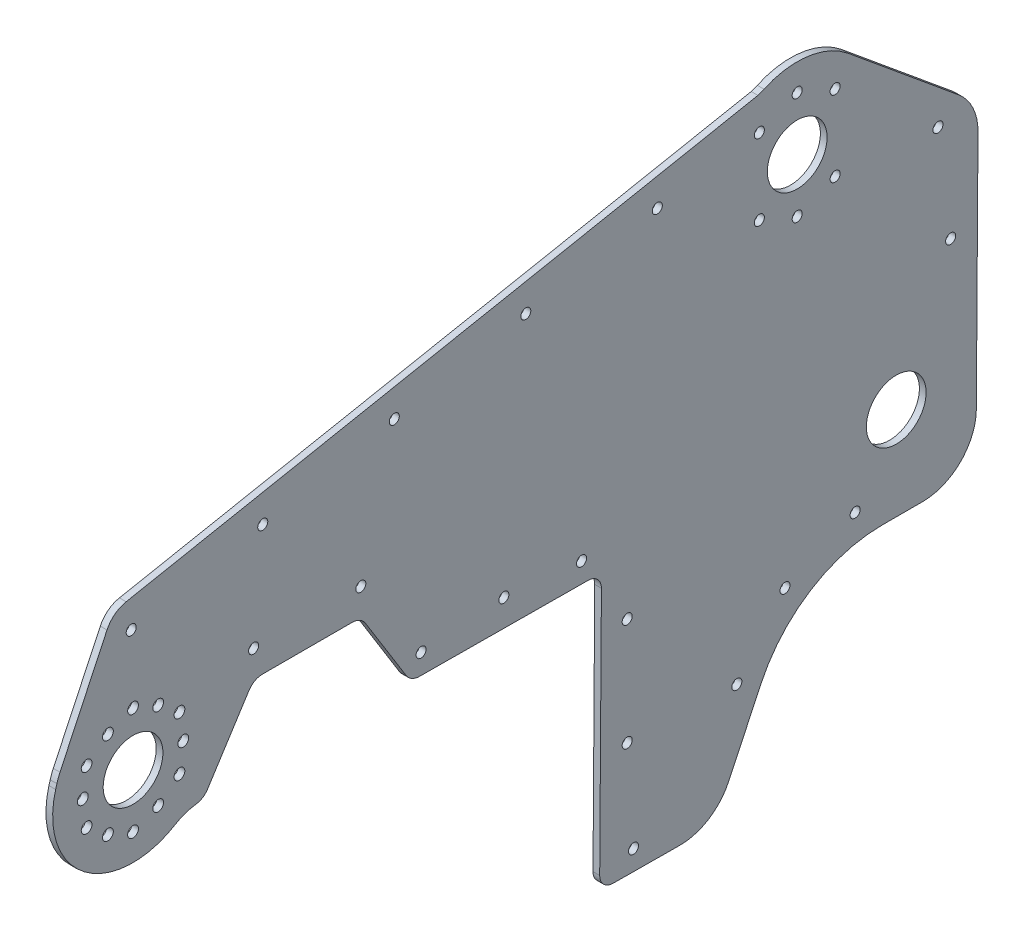
SolidWorks part; units mm, degrees
material "Hexcel AS4C (3000 Filaments)"
ref_plane "Front Plane" through (0, 0, 0) normal (0, 0, 1) x (1, 0, 0)
ref_plane "Top Plane" through (0, 0, 0) normal (0, 1, 0) x (1, 0, 0)
ref_plane "Right Plane" through (0, 0, 0) normal (1, 0, 0) x (0, 0, -1)
sketch "Sketch1" plane through (2085.2745, 0, 0) normal (-1, 0, 0) x (0, 0, 1)
  line L0 (-470.4626, 294.284) -> (-813.3543, 291.9025) construction
  line L1 (-819.6601, 285.5085) -> (-816.3083, -197.0799) construction
  line L2 (-816.3083, -197.0799) -> (-644.8624, -195.8891) construction
  line L3 (-638.5567, -189.4951) -> (-639.3726, -72.023) construction
  line L4 (-633.0668, -65.629) -> (-442.3722, -64.3046) construction
  line L5 (-380.6906, -25.2502) -> (-470.4626, 294.284) construction
  line L6 (-470.4626, 294.284) -> (-813.3543, 291.9025) construction
  line L7 (-819.6601, 285.5085) -> (-818.6898, 145.8119) construction
  line L8 (-676.4765, -196.1087) -> (-644.8624, -195.8891)
  line L9 (-638.5567, -189.4951) -> (-639.3726, -72.023)
  line L10 (-633.0668, -65.629) -> (-553.1901, -65.0743)
  line L11 (-380.6906, -25.2502) -> (-381.2742, -23.1727)
  line L12 (-406.6004, 23.1935) -> (-802.249, 140.9199) construction
  line L14 (-756.4363, 89.0125) -> (-808.6343, 45.9004)
  line L15 (-817.8587, 26.1401) -> (-817.0703, -87.3715)
  line L16 (-818.5707, 128.6591) -> (-817.9425, 38.2125) construction
  line L17 (-393.1787, 19.1998) -> (-470.4626, 294.284) construction
  line L18 (-699.6149, -181.5678) -> (-715.0401, -148.9488)
  line L19 (-772.4451, -112.5951) -> (-791.6709, -112.5951)
  line L20 (-816.8951, -112.5951) -> (-816.3083, -197.0799) construction
  line L21 (-816.3083, -197.0799) -> (-692.6854, -196.2212) construction
  line L22 (-530.97, 35.9025) -> (-713.5248, 93.2198) construction
  line L23 (-384.9948, -9.9298) -> (-389.3911, 5.7185) construction
  line L24 (-546.7673, -61.4706) -> (-527.5902, -30.5489)
  line L25 (-521.1144, -26.945) -> (-478.7266, -26.945)
  line L26 (-472.3074, -30.4591) -> (-452.7015, -61.1107)
  line L27 (-405.0283, 28.0353) -> (-382.753, -19.2109)
  line L28 (-475.9205, -39.5052) -> (-523.9205, -39.5052) construction
  line L29 (-475.9205, -39.5052) -> (-523.9205, -39.5052) construction
  line L30 (-548.9841, -65.045) -> (-450.6219, -64.3619) construction
  line L31 (-527.1657, 35.3193) -> (-416.5156, 35.3193) construction
  line L32 (-398.1188, -5.8092) -> (-529.1126, 35.3193) construction
  line L33 (-713.5248, 93.2198) -> (-414.0951, 35.0865)
  line L34 (-792.0032, 59.6366) -> (-540.5464, 59.6366) construction
  arc A0 (-813.3543, 291.9025) -> (-819.6601, 285.5085) centre (-813.3102, 285.5526) ccw construction
  arc A1 (-644.8624, -195.8891) -> (-638.5567, -189.4951) centre (-644.9065, -189.5392) ccw construction
  arc A2 (-633.0668, -65.629) -> (-639.3726, -72.023) centre (-633.0227, -71.9789) ccw construction
  arc A3 (-442.3722, -64.3046) -> (-380.6906, -25.2502) centre (-417.3705, -35.5552) ccw construction
  arc A4 (-813.3543, 291.9025) -> (-819.6601, 285.5085) centre (-813.3102, 285.5526) ccw construction
  arc A5 (-644.8624, -195.8891) -> (-638.5567, -189.4951) centre (-644.9065, -189.5392) ccw
  arc A6 (-633.0668, -65.629) -> (-639.3726, -72.023) centre (-633.0227, -71.9789) ccw
  arc A7 (-437.2155, -68.0789) -> (-380.6906, -25.2502) centre (-417.3705, -35.5552) ccw
  arc A8 (-406.6004, 23.1935) -> (-389.3911, 5.7185) centre (-413.8444, -1.1516) cw construction
  arc A11 (-715.0401, -148.9488) -> (-772.4451, -112.5951) centre (-772.4451, -176.0951) ccw
  arc A12 (-699.6149, -181.5678) -> (-676.4765, -196.1087) centre (-676.6529, -170.7093) ccw
  arc A13 (-791.6709, -112.5951) -> (-817.0703, -87.3715) centre (-791.6709, -87.1951) cw
  arc A14 (-802.249, 140.9199) -> (-818.5707, 128.6591) centre (-805.871, 128.7473) ccw construction
  circle A16 centre (-732.1738, 59.6366) radius 14.1605
  circle A17 centre (-779.0999, -68.5703) radius 14.1605
  circle A18 centre (-654.5854, -186.4314) radius 2.3812
  circle A19 centre (-629.9581, -56.0822) radius 2.3812
  circle A20 centre (-553.8955, -55.5539) radius 2.3812
  circle A21 centre (-417.3705, -35.5552) radius 14.1605
  arc A22 (-716.4192, 94.3267) -> (-756.4363, 89.0125) centre (-732.1738, 59.6366) ccw
  arc A23 (-382.753, -19.2109) -> (-381.2742, -23.1727) centre (-405.7275, -30.0428) cw
  arc A24 (-713.5248, 93.2198) -> (-716.4192, 94.3267) centre (-705.9161, 117.4534) cw
  arc A25 (-808.6343, 45.9004) -> (-817.8587, 26.1401) centre (-792.4593, 26.3165) ccw
  arc A26 (-447.2431, -64.564) -> (-437.2155, -68.0789) centre (-450.4455, -89.7613) cw
  arc A27 (-452.7015, -61.1107) -> (-447.2431, -64.564) centre (-446.2823, -57.0048) ccw
  arc A28 (-546.7673, -61.4706) -> (-553.1901, -65.0743) centre (-553.243, -57.4544) cw
  arc A29 (-478.7266, -26.945) -> (-472.3074, -30.4591) centre (-478.7266, -34.565) cw
  arc A30 (-527.5902, -30.5489) -> (-521.1144, -26.945) centre (-521.1144, -34.565) cw
  arc A31 (-398.1188, -5.8092) -> (-382.753, -19.2109) centre (-405.7275, -30.0428) cw construction
  arc A32 (-527.1657, 35.3193) -> (-530.97, 35.9025) centre (-527.1657, 48.0193) cw construction
  arc A33 (-414.0951, 35.0865) -> (-405.0283, 28.0353) centre (-416.5156, 22.6193) cw
  arc A34 (-416.5156, 35.3193) -> (-414.0951, 35.0865) centre (-416.5156, 22.6193) cw construction
  point P63 (-715.1948, 93.7441)
  point P77 (-499.9205, -26.945)
  point P78 (-499.9205, -39.5052)
  point P87 (-474.5551, -26.945)
  point P90 (-525.3551, -26.945)
  point P96 (-408.4626, 35.3193)
  dimension "D5" = 25.4
  dimension "D8" = 63.5
  dimension "D10" = 25.4
  dimension "D3" = 12.7
  dimension "D4" = 28.321
  dimension "D11" = 38.1
  dimension "D15" = 25.4
  dimension "D16" = 25.4
  dimension "D19" = 7.62
  dimension "D22" = 12.7
  dimension "D23" = 4.7625
  dimension "D1" = 44.45
  dimension "D2" = 146.05
  dimension "D6" = 44.45
  dimension "D7" = 38.1
  dimension "D9" = 76.2
  dimension "D12" = 50.8
  dimension "D13" = 330.2
  dimension "D14" = 53.975
  dimension "D17" = 50.8
  dimension "D18" = 38.1
  dimension "D20" = 60.287
  dimension "D21" = 120.65
  dimension "D24" = 172.2317
  dimension "D25" = 136.525
  dimension "D26" = 69.9712
  dimension "D27" = 126.23
extrude "Boss-Extrude2" add sketch "Sketch1" along normal blind 3.175
sketch "Sketch2" plane through (2085.2745, 0, 0) normal (1, 0, 0) x (0, 0, -1)
  circle A0 centre (732.1738, 59.6366) radius 14.1605 construction
  circle A1 centre (732.1738, 59.6366) radius 14.1605 construction
  circle A2 centre (732.1738, 85.0366) radius 2.3812
  circle A3 centre (732.1738, 34.2366) radius 2.3812
  circle A4 centre (750.1343, 41.676) radius 2.3812
  circle A5 centre (714.2134, 77.5972) radius 2.3812
  circle A6 centre (732.1738, 59.6366) radius 25.4 construction
  circle A7 centre (750.1343, 77.5972) radius 2.3812
  circle A8 centre (714.2134, 41.676) radius 2.3812
  dimension "D1" = 50.8
  dimension "D2" = 4.7625
  dimension "D3" = 7.4394
  dimension "D4" = 7.4394
extrude "Cut-Extrude1" cut sketch "Sketch2" against normal through all
sketch "Sketch3" plane through (2085.2745, 0, 0) normal (1, 0, 0) x (0, 0, -1)
  circle A1 centre (759.6181, -100.9825) radius 2.3813
  circle A2 centre (759.6181, -100.9825) radius 2.3813
  circle A3 centre (541.1877, 46.532) radius 2.3813
  circle A4 centre (541.1877, 46.532) radius 2.3812
  circle A5 centre (478.8516, 34.4297) radius 2.3813
  circle A6 centre (478.8516, 34.4297) radius 2.3813
  circle A7 centre (416.5156, 22.3274) radius 2.3813
  circle A8 centre (416.5156, 22.3274) radius 2.3813
  circle A9 centre (525.3205, -14.245) radius 2.3813
  circle A10 centre (525.3205, -14.245) radius 2.3813
  circle A11 centre (798.8869, 37.4794) radius 2.3813
  circle A12 centre (798.8869, 37.4794) radius 2.3813
  circle A13 centre (665.8598, 70.7367) radius 2.3813
  circle A14 centre (665.8598, 70.7367) radius 2.3812
  circle A15 centre (603.5237, 58.6344) radius 2.3813
  circle A16 centre (603.5237, 58.6344) radius 2.3812
  circle A17 centre (703.5591, -143.5195) radius 2.3813
  circle A18 centre (703.5591, -143.5195) radius 2.3813
  circle A19 centre (726.3842, -115.3922) radius 2.3813
  circle A20 centre (726.3842, -115.3922) radius 2.3813
  circle A21 centre (804.8987, -11.2496) radius 2.3813
  circle A22 centre (804.8987, -11.2496) radius 2.3813
  circle A23 centre (474.5205, -14.245) radius 2.3813
  circle A24 centre (474.5205, -14.245) radius 2.3813
  circle A25 centre (651.59, -141.5513) radius 2.3813
  circle A26 centre (651.59, -141.5513) radius 2.3813
  circle A27 centre (651.59, -90.7513) radius 2.3813
  circle A28 centre (651.59, -90.7513) radius 2.3813
  circle A29 centre (593.1285, -52.6513) radius 2.3813
  circle A30 centre (593.1285, -52.6513) radius 2.3813
  dimension "D1" = 0
  dimension "D2" = 0
  dimension "D3" = 0
  dimension "D4" = 0
  dimension "D5" = 0
  dimension "D6" = 0
  dimension "D7" = 0
  dimension "D8" = 0
  dimension "D9" = 0
  dimension "D10" = 0
  dimension "D11" = 0
  dimension "D12" = 0
  dimension "D13" = 0
  dimension "D14" = 0
  dimension "D15" = 0
extrude "Cut-Extrude2" cut sketch "Sketch3" against normal up to surface (3.175 mm away) up to face at (2082.0995, 85.0366, -734.5551)
sketch "Sketch4" plane through (2085.2745, 0, 0) normal (1, 0, 0) x (0, 0, -1)
  circle A0 centre (417.3705, -35.5552) radius 14.1605 construction
  circle A1 centre (417.3705, -35.5552) radius 14.1605 construction
sketch "Sketch5" plane through (2085.2745, 0, 0) normal (1, 0, 0) x (0, 0, -1)
  line L0 (-4.7879, -2.7643) -> (0, -5.5286)
  line L1 (0, -5.5286) -> (4.7879, -2.7643)
  line L2 (4.7879, -2.7643) -> (4.7879, 2.7643)
  line L3 (4.7879, 2.7643) -> (0, 5.5286)
  line L4 (0, 5.5286) -> (-4.7879, 2.7643)
  line L5 (-4.7879, 2.7643) -> (-4.7879, -2.7643)
  circle A0 centre (-11.9062, 20.6222) radius 2.5527
  circle A1 centre (0, 25.4) radius 2.5527
  circle A2 centre (-23.8125, 0) radius 2.5527
  circle A3 centre (-21.997, 12.7) radius 2.5527
  circle A4 centre (-11.9062, -20.6222) radius 2.5527
  circle A5 centre (-21.997, -12.7) radius 2.5527
  circle A6 centre (11.9062, -20.6222) radius 2.5527
  circle A7 centre (0, -25.4) radius 2.5527
  circle A8 centre (23.8125, 0) radius 2.5527
  circle A9 centre (21.997, -12.7) radius 2.5527
  circle A10 centre (11.9062, 20.6222) radius 2.5527
  circle A11 centre (21.997, 12.7) radius 2.5527
  circle A12 centre (0, 0) radius 30.1625
sketch "Sketch6" plane through (2085.2745, 0, 0) normal (1, 0, 0) x (0, 0, -1)
  line L0 (405.4643, -14.933) -> (393.558, -35.5552) construction
  line L1 (393.558, -35.5552) -> (405.4643, -56.1775) construction
  line L2 (405.4643, -56.1775) -> (429.2768, -56.1775) construction
  line L3 (429.2768, -56.1775) -> (441.183, -35.5552) construction
  line L4 (441.183, -35.5552) -> (429.2768, -14.933) construction
  line L5 (429.2768, -14.933) -> (405.4643, -14.933) construction
  line L6 (395.3735, -22.8552) -> (417.3705, -10.1552) construction
  line L7 (417.3705, -10.1552) -> (439.3675, -22.8552) construction
  line L8 (439.3675, -22.8552) -> (439.3675, -48.2552) construction
  line L9 (439.3675, -48.2552) -> (417.3705, -60.9552) construction
  line L10 (417.3705, -60.9552) -> (395.3735, -48.2552) construction
  line L11 (395.3735, -48.2552) -> (395.3735, -22.8552) construction
  circle A0 centre (417.3705, -35.5552) radius 23.8125 construction
  circle A1 centre (417.3705, -35.5552) radius 25.4 construction
  circle A2 centre (395.3735, -48.2552) radius 2.5527
  circle A3 centre (417.3705, -35.5552) radius 14.1605 construction
  circle A4 centre (405.4643, -56.1775) radius 2.5527
  circle A6 centre (395.3735, -22.8552) radius 2.5527
  circle A8 centre (393.558, -35.5552) radius 2.5527
  circle A10 centre (417.3705, -10.1552) radius 2.5527
  circle A12 centre (405.4643, -14.933) radius 2.5527
  circle A14 centre (439.3675, -22.8552) radius 2.5527
  circle A16 centre (429.2768, -14.933) radius 2.5527
  circle A18 centre (439.3675, -48.2552) radius 2.5527
  circle A20 centre (441.183, -35.5552) radius 2.5527
  circle A22 centre (417.3705, -60.9552) radius 2.5527
  circle A24 centre (429.2768, -56.1775) radius 2.5527
  dimension "D1" = 50.8
  dimension "D2" = 47.625
  dimension "D3" = 5.1054
extrude "Cut-Extrude3" cut sketch "Sketch6" against normal through all
